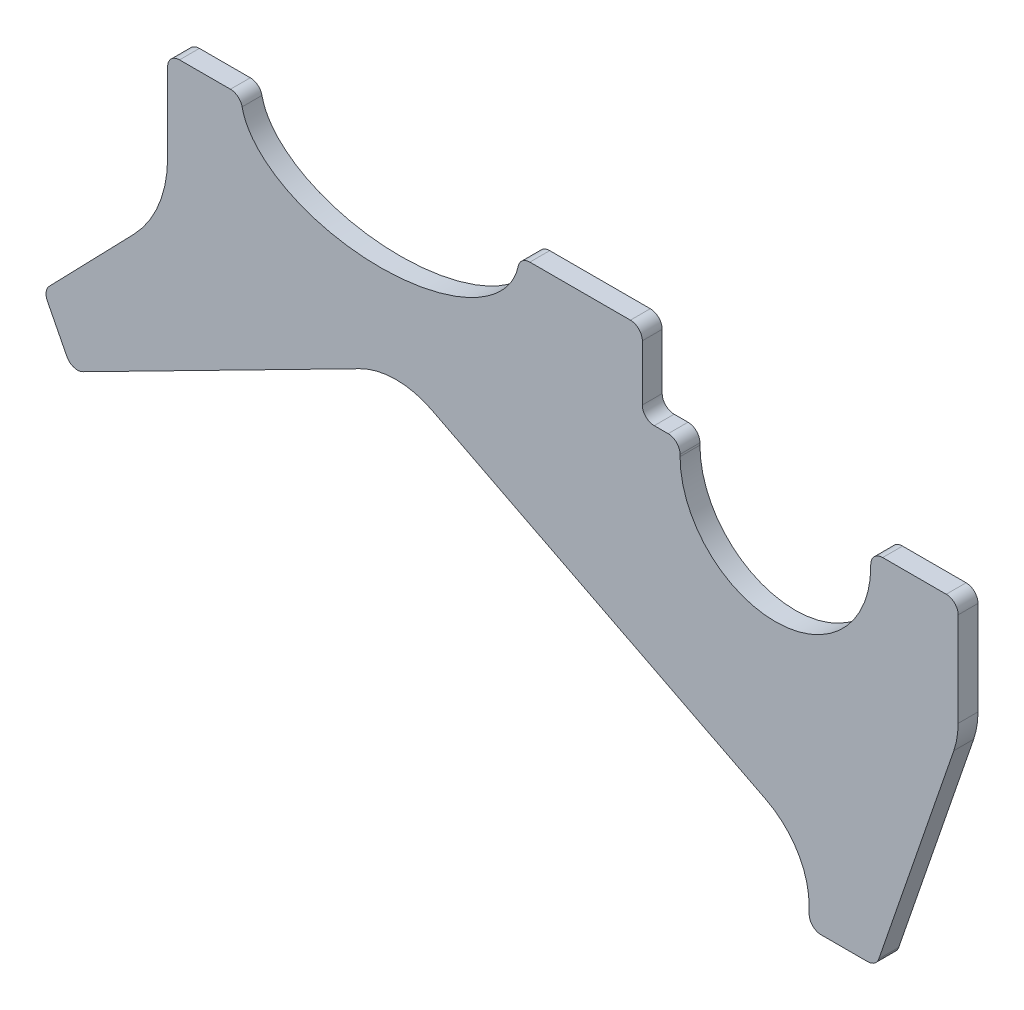
SolidWorks part; units mm, degrees
ref_plane "Plane1" through (0, 0, 0) normal (0, 0, 1) x (1, 0, 0)
ref_plane "Plane2" through (0, 0, 0) normal (0, 1, 0) x (1, 0, 0)
ref_plane "Plane3" through (0, 0, 0) normal (1, 0, 0) x (0, 0, -1)
sketch "Sketch1" plane through (0, 0, 0) normal (0, 0, 1) x (1, 0, 0)
  line L0 (9.0798, -4.6264) -> (93.0798, -47.4265)
  line L1 (121.537, -67.9767) -> (140.4104, -13.1645)
  line L2 (141.5, -6.6531) -> (141.5, 17)
  line L3 (138.5, 20) -> (122.5, 20)
  line L4 (62, 37) -> (62, 23)
  line L5 (0, 0) -> (0, -41.1004) construction
  line L6 (-9.0798, -4.6264) -> (-78.827, -40.1644)
  line L7 (33.6865, 40) -> (59, 40)
  line L8 (118.7005, -70) -> (107, -70)
  line L9 (104, -67) -> (104, -65.2467)
  line L10 (-65.9535, -3.7256) -> (-87.2723, -25.7307)
  line L11 (-57.5, 17.149) -> (-57.5, 37)
  line L12 (-54.5, 40) -> (-41.6865, 40)
  line L13 (-87.7907, -29.1801) -> (-82.862, -38.8533)
  line L14 (95.5, 20) -> (95.5, 39.1418) construction
  line L15 (65, 20) -> (68.5, 20)
  line L16 (119.5, 16.5) -> (119.5, 17)
  line L17 (71.5, 16.5) -> (71.5, 17)
  arc A0 (9.0798, -4.6264) -> (-9.0798, -4.6264) centre (0, -22.4465) ccw
  arc A1 (-57.5, 37) -> (-54.5, 40) centre (-54.5, 37) cw
  arc A2 (-38.7506, 37.6167) -> (-41.6865, 40) centre (-41.6865, 37) ccw
  arc A3 (30.7506, 37.6167) -> (33.6865, 40) centre (33.6865, 37) cw
  arc A4 (59, 40) -> (62, 37) centre (59, 37) cw
  arc A5 (62, 23) -> (65, 20) centre (65, 23) ccw
  arc A6 (141.5, 17) -> (138.5, 20) centre (138.5, 17) ccw
  arc A7 (71.5, 17) -> (68.5, 20) centre (68.5, 17) ccw
  arc A8 (104, -65.2467) -> (93.0798, -47.4265) centre (84, -65.2467) ccw
  arc A9 (118.7005, -70) -> (121.537, -67.9767) centre (118.7005, -67) ccw
  arc A10 (107, -70) -> (104, -67) centre (107, -67) cw
  arc A11 (-78.827, -40.1644) -> (-82.862, -38.8533) centre (-80.189, -37.4913) cw
  arc A12 (-87.2723, -25.7307) -> (-87.7907, -29.1801) centre (-85.1177, -27.8182) ccw
  arc A13 (-65.9535, -3.7256) -> (-57.5, 17.149) centre (-87.5, 17.149) ccw
  arc A14 (140.4104, -13.1645) -> (141.5, -6.6531) centre (121.5, -6.6531) ccw
  arc A15 (119.5, 17) -> (122.5, 20) centre (122.5, 17) cw
  arc A16 (119.5, 16.5) -> (71.5, 16.5) centre (95.5, 16.5) cw
  ellipse E0 centre (-4, 40) end of major axis (31, 40) minor radius 20 (-38.7506, 37.6167) -> (30.7506, 37.6167) ccw
  point P45 (-81.5, -41.5263)
  point P51 (-88.7638, -27.2702)
  point P54 (-57.5, 5)
  point P57 (141.5, -10)
  dimension "D15" = 20
  dimension "D11" = 3
  dimension "D10" = 3
  dimension "D13" = 31
  dimension "D19" = 20
  dimension "D20" = 3
  dimension "D21" = 24
  dimension "D24" = 3
  dimension "D25" = 30
  dimension "D26" = 20
  dimension "D28" = 3
  dimension "D29" = 24
  dimension "D30" = 47.5
  dimension "D1" = 63
  dimension "D2" = 63
  dimension "D4" = 57.5
  dimension "D5" = 20
  dimension "D6" = 141.5
  dimension "D7" = 19
  dimension "D8" = 30
  dimension "D9" = 46
  dimension "D12" = 70
  dimension "D14" = 20
  dimension "D16" = 53.5
  dimension "D17" = 90
  dimension "D18" = 104
  dimension "D22" = 16
  dimension "D23" = 35
  dimension "D27" = 20
extrude "Extrude1" add sketch "Sketch1" along normal blind 5
